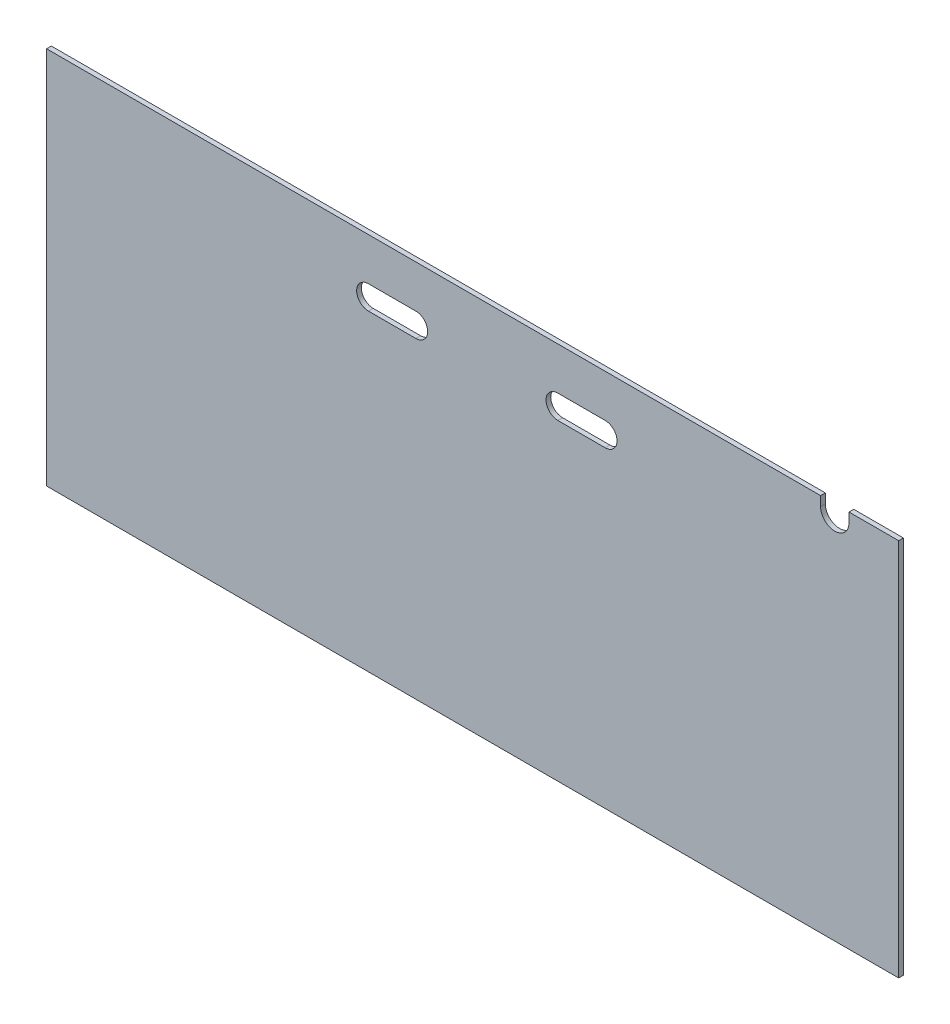
SolidWorks part; units mm, degrees
material "PC High Viscosity"
ref_plane "Front Plane" through (0, 0, 0) normal (0, 0, 1) x (1, 0, 0)
ref_plane "Top Plane" through (0, 0, 0) normal (0, 1, 0) x (1, 0, 0)
ref_plane "Right Plane" through (0, 0, 0) normal (1, 0, 0) x (0, 0, -1)
sketch "Sketch1" plane through (0, 0, 0) normal (0, 0, 1) x (1, 0, 0)
  line L1 (0, 0) -> (1143, 0)
  line L2 (0, 0) -> (0, 508)
  line L3 (0, 508) -> (1143, 508)
  line L4 (1143, 0) -> (1143, 508)
  dimension "D1" = 508
  dimension "D2" = 1143
extrude "Boss-Extrude1" add sketch "Sketch1" along normal blind 6.35
sketch "Sketch2" plane through (0, 0, 6.35) normal (0, 0, 1) x (1, 0, 0)
  line L0 (431.8, 434.975) -> (495.3, 434.975) construction
  line L1 (431.8, 450.85) -> (495.3, 450.85)
  line L2 (431.8, 419.1) -> (495.3, 419.1)
  line L3 (685.8, 434.975) -> (749.3, 434.975) construction
  line L4 (685.8, 450.85) -> (749.3, 450.85)
  line L5 (685.8, 419.1) -> (749.3, 419.1)
  line L6 (1143, 0) -> (1143, 508) construction
  line L7 (1143, 508) -> (0, 508) construction
  arc A0 (431.8, 450.85) -> (431.8, 419.1) centre (431.8, 434.975) ccw
  arc A1 (495.3, 419.1) -> (495.3, 450.85) centre (495.3, 434.975) ccw
  arc A2 (685.8, 450.85) -> (685.8, 419.1) centre (685.8, 434.975) ccw
  arc A3 (749.3, 419.1) -> (749.3, 450.85) centre (749.3, 434.975) ccw
  point P2 (463.55, 434.975)
  point P7 (717.55, 434.975)
  dimension "D5" = 15.875
  dimension "D1" = 393.7
  dimension "D2" = 457.2
  dimension "D3" = 647.7
  dimension "D4" = 711.2
  dimension "D6" = 73.025
extrude "Cut-Extrude1" cut sketch "Sketch2" against normal through all
hole_wizard "CSK for 1/4 Flat Head Machine Screw1" positions "Sketch3" profile "Sketch5" countersink size "1/4" standard "ANSI Inch"
sketch "Sketch3" plane through (0, 0, 6.35) normal (0, 0, 1) x (1, 0, 0)
  line L0 (1143, 508) -> (0, 508) construction
  line L1 (1143, 0) -> (1143, 508) construction
  line L2 (1143, 508) -> (0, 508) construction
  point P0 (914.4, 434.975)
  point P2 (812.8, 434.975)
  point P4 (368.3, 434.975)
  point P6 (266.7, 434.975)
  point P8 (1120.775, 107.95)
  point P10 (1101.725, 88.9)
  point P12 (41.275, 107.95)
  point P14 (22.225, 88.9)
  dimension "D1" = 73.025
  dimension "D2" = 228.6
  dimension "D3" = 330.2
  dimension "D4" = 774.7
  dimension "D5" = 876.3
  dimension "D6" = 400.05
  dimension "D7" = 419.1
  dimension "D8" = 22.225
  dimension "D9" = 41.275
  dimension "D10" = 1101.725
  dimension "D11" = 1120.775
sketch "Sketch5" plane through (914.4, 434.975, 6.35) normal (1, 0, 0) x (0, -1, 0)
  line L0 (0, 0) -> (0, 6.35)
  line L1 (0, 6.35) -> (3.3782, 6.35)
  line L2 (3.3782, 6.35) -> (3.3782, 3.5209)
  line L3 (3.3782, 3.5209) -> (6.4389, 0)
  line L5 (6.4389, 0) -> (0, 0)
  line L6 (-3.3782, 3.5209) -> (-6.4389, 0) construction
  line L11 (0, -6.35) -> (0, 107.95) construction
  dimension "Thru Hole Dia." = 6.7564
  dimension "Thru Hole Depth" = 6.35
  dimension "Near C'Sink Dia." = 12.8778
  dimension "Near C'Sink Angle" = 82
sketch "Sketch6" plane through (0, 0, 6.35) normal (0, 0, 1) x (1, 0, 0)
  line L0 (1143, 508) -> (0, 508) construction
  line L1 (1038.225, 508) -> (1076.325, 508)
  line L2 (1038.225, 508) -> (1038.225, 495.3)
  line L4 (1076.325, 508) -> (1076.325, 495.3)
  line L5 (1143, 0) -> (1143, 508) construction
  arc A0 (1076.325, 495.3) -> (1038.225, 495.3) centre (1057.275, 495.3) cw
  dimension "D3" = 104.775
  dimension "D1" = 12.7
  dimension "D2" = 66.675
extrude "Cut-Extrude2" cut sketch "Sketch6" against normal through all
